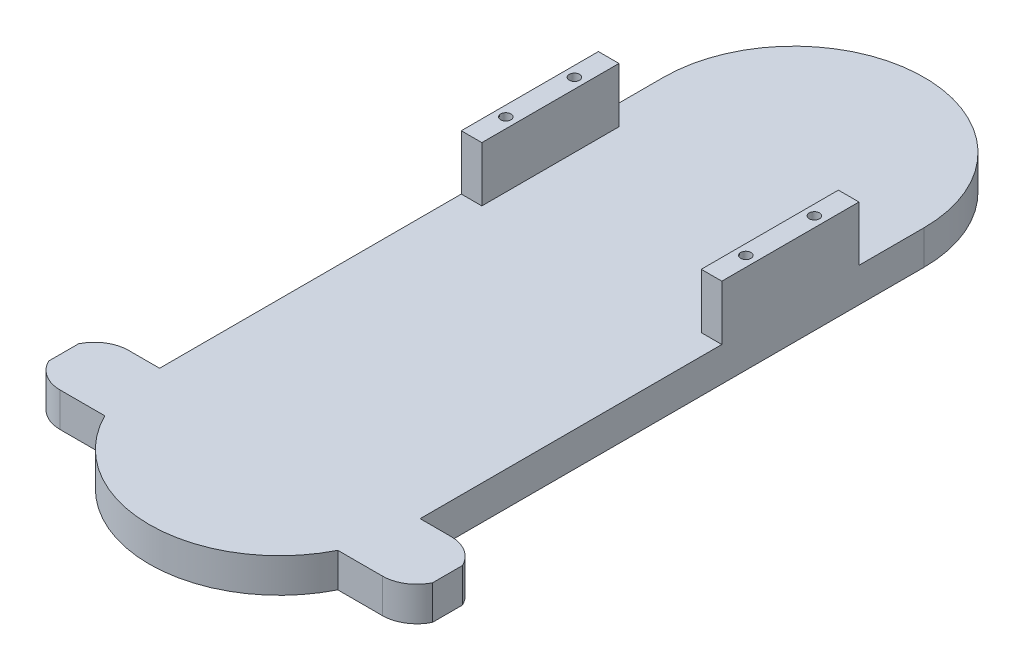
SolidWorks part; units mm, degrees
ref_plane "Front" through (0, 0, 0) normal (0, 0, 1) x (1, 0, 0)
ref_plane "Top" through (0, 0, 0) normal (0, 1, 0) x (1, 0, 0)
ref_plane "Right" through (0, 0, 0) normal (1, 0, 0) x (0, 0, -1)
sketch "草图1" plane through (0, 0, 0) normal (0, 1, 0) x (1, 0, 0)
  line L0 (0, 24.0367) -> (0, 0) construction
  line L1 (0, 0) -> (-31.1152, 0) construction
  line L2 (0, -75) -> (0, 75) construction
  line L3 (-38, -75) -> (-38, 75)
  line L4 (38, -75) -> (38, 75)
  arc A0 (-38, -75) -> (38, -75) centre (0, -75) ccw
  arc A1 (38, 75) -> (-38, 75) centre (0, 75) ccw
  point P6 (0, 0)
extrude "凸台-拉伸1" add sketch "草图1" along normal blind 10
sketch "草图3" plane through (0, 10, 0) normal (0, 1, 0) x (1, 0, 0)
  line L0 (-87.6038, -64) -> (61.1928, -64) construction
  line L1 (-38, 75) -> (-38, -75) construction
  line L2 (-38, -64) -> (-30, -64)
  line L3 (-38, -64) -> (-38, -4)
  line L4 (-38, -4) -> (-30, -4)
  line L5 (-30, -64) -> (-30, -4)
  line L6 (38, -75) -> (38, 75) construction
  line L7 (38, -64) -> (30, -64)
  line L8 (38, -64) -> (38, -4)
  line L9 (38, -4) -> (30, -4)
  line L10 (30, -64) -> (30, -4)
  dimension "D1" = 64
  dimension "D2" = 60
  dimension "D3" = 8
  dimension "D4" = 8
  dimension "D5" = 60
sketch "草图4" plane through (0, 10, 0) normal (0, 1, 0) x (1, 0, 0)
  line L0 (-57.3538, 16) -> (64.3655, 16) construction
  line L1 (-38, 75) -> (-38, -75) construction
  line L2 (-38, 16) -> (-32, 16)
  line L3 (-38, 16) -> (-38, 56)
  line L4 (-38, 56) -> (-32, 56)
  line L5 (-32, 16) -> (-32, 56)
  line L6 (38, -75) -> (38, 75) construction
  line L7 (38, 16) -> (32, 16)
  line L8 (38, 16) -> (38, 56)
  line L9 (38, 56) -> (32, 56)
  line L10 (32, 16) -> (32, 56)
  dimension "D1" = 16
  dimension "D2" = 6
  dimension "D3" = 40
  dimension "D4" = 6
extrude "凸台-拉伸3" add sketch "草图4" along normal blind 16
sketch "草图7" plane through (0, 26, 0) normal (0, 1, 0) x (1, 0, 0)
  line L0 (-38, 36) -> (38, 36) construction
  line L1 (-38, 56) -> (-38, 16) construction
  line L2 (38, 16) -> (38, 56) construction
  line L3 (-32, 16) -> (-32, 56) construction
  line L4 (-38, 16) -> (-32, 16) construction
  line L5 (35, 16) -> (35, 56) construction
  line L6 (32, 16) -> (38, 16) construction
  line L7 (38, 56) -> (32, 56) construction
  circle A0 centre (-35, 26) radius 1.5
  circle A1 centre (-35, 46) radius 1.5
  circle A2 centre (35, 26) radius 1.5
  circle A3 centre (35, 46) radius 1.5
  point P6 (-32, 36)
  dimension "D2" = 20
  dimension "D1" = 10
extrude "切除-拉伸3" cut sketch "草图7" against normal blind 10
sketch "草图8" plane through (0, 10, 0) normal (0, 1, 0) x (1, 0, 0)
  line L1 (-47, -72) -> (47, -72)
  line L2 (-56, -77.6411) -> (-56, -86.3589)
  line L3 (-47, -92) -> (47, -92)
  line L4 (56, -77.6411) -> (56, -86.3589)
  arc A0 (-47, -72) -> (-56, -77.6411) centre (-47, -82) ccw
  arc A1 (47, -92) -> (56, -86.3589) centre (47, -82) ccw
  arc A2 (-56, -86.3589) -> (-47, -92) centre (-47, -82) ccw
  arc A3 (56, -77.6411) -> (47, -72) centre (47, -82) ccw
  dimension "D1" = 20
  dimension "D2" = 72
  dimension "D3" = 112
  dimension "D4" = 56
extrude "凸台-拉伸4" add sketch "草图8" against normal blind 10
